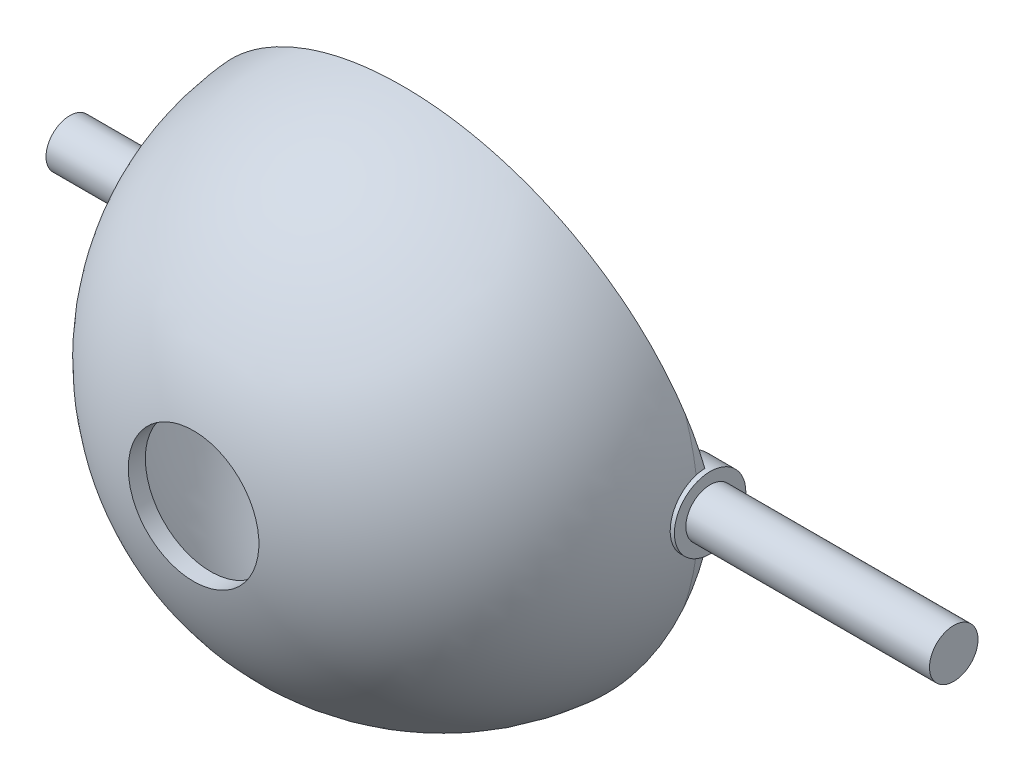
SolidWorks part; units mm, degrees
ref_plane "Front Plane" through (0, 0, 0) normal (0, 0, 1) x (1, 0, 0)
ref_plane "Top Plane" through (0, 0, 0) normal (0, 1, 0) x (1, 0, 0)
ref_plane "Right Plane" through (0, 0, 0) normal (1, 0, 0) x (0, 0, -1)
sketch "Sketch1" plane through (0, 0, 0) normal (0, 0, 1) x (1, 0, 0)
  circle A0 centre (0, 0) radius 27.95
extrude "Boss-Extrude1" add sketch "Sketch1" along normal blind 27.6202
fillet "Fillet1" radius 26.67 1 edges at (27.95, 0, 27.6202)
shell "Shell1" thickness 1.778
sketch "Sketch3" plane through (0, 0, 0) normal (0, 0, -1) x (-1, 0, 0)
  line L1 (-28.5123, -1.3772) -> (-25.5345, -1.3772)
  line L2 (-28.5123, -1.3772) -> (-28.5123, 1.3772)
  line L3 (-28.5123, 1.3772) -> (-25.5345, 1.3772)
  line L4 (-25.5345, -1.3772) -> (-25.5345, 1.3772)
  line L5 (-28.5123, -1.3772) -> (-25.5345, 1.3772) construction
  line L6 (-28.5123, 1.3772) -> (-25.5345, -1.3772) construction
  point P0 (-27.0234, 0)
extrude "Boss-Extrude3" add sketch "Sketch3" along normal blind 1.016
sketch "Sketch4" plane through (28.5123, 0, 0) normal (1, 0, 0) x (0, 0, -1)
  circle A0 centre (0, 0) radius 3.8203
extrude "Boss-Extrude4" add sketch "Sketch4" against normal blind 68.7609 and the other way blind 25.7903 contours A0
sketch "Sketch5" plane through (-40.2486, 0, 0) normal (-1, 0, 0) x (0, 0, 1)
  circle A1 centre (0, 0) radius 1.0579
extrude "Cut-Extrude1" cut sketch "Sketch5" against normal blind 74.422
sketch "Sketch6" plane through (-40.2486, 0, 0) normal (-1, 0, 0) x (0, 0, 1)
  circle A0 centre (0, 0) radius 4.4527
  circle A1 centre (0, 0) radius 2.5419
extrude "Cut-Extrude2" cut sketch "Sketch6" against normal blind 12.446 contours A1 | A0
sketch "Sketch7" plane through (54.3025, 0, 0) normal (1, 0, 0) x (0, 0, -1)
  circle A0 centre (0, 0) radius 4.5798
  circle A1 centre (0, 0) radius 2.5953
extrude "Cut-Extrude3" cut sketch "Sketch7" against normal blind 26.058 contours A1 | A0
sketch "Sketch9" plane through (0, 0, 0) normal (0, 0, -1) x (-1, 0, 0)
  circle A0 centre (0, 0) radius 25.3275
extrude "Cut-Extrude4" cut sketch "Sketch9" against normal blind 4.572 and the other way blind 8.128
sketch "Sketch10" plane through (0, 0, 27.6202) normal (0, 0, 1) x (1, 0, 0)
  circle A0 centre (0, 0) radius 6.985
extrude "Cut-Extrude5" cut sketch "Sketch10" against normal blind 5.588 contours A0
sketch3d "3DSketch1"
  circle A0 centre (0, 0, 27.0029) radius 6.985 construction
  point P2 (0, 0, 33.9879)
sketch "Sketch11" plane through (0, 0, 27.0029) normal (0, 0, 1) x (1, 0, 0)
  circle A0 centre (0, 0) radius 0.9577
extrude "Boss-Extrude5" add sketch "Sketch11" against normal blind 22.86 separate body contours A0
sketch "Sketch12" plane through (0, 0, 4.1429) normal (0, 0, -1) x (-1, 0, 0)
  line L0 (0, 0) -> (0, 16.6384)
  line L1 (0, 16.6384) -> (11.938, 16.6384)
  line L2 (0, 0) -> (0, -16.6384)
  line L3 (0, -16.6384) -> (-11.9535, -16.6384)
  circle A0 centre (11.938, 16.6384) radius 3.048
  circle A1 centre (-11.9535, -16.6384) radius 3.048
extrude "Boss-Extrude6" add sketch "Sketch12" against normal blind 11.3629 separate body contours A0 | A1
sketch "Sketch14" plane through (0, 0, 0) normal (0, 0, -1) x (-1, 0, 0)
  circle A0 centre (0, 0) radius 27.95
  circle A1 centre (0, 0) radius 2.1119
extrude "Cut-Extrude6" cut sketch "Sketch14" against normal blind 33.274 contours A1
sketch "Sketch15" plane through (54.3025, 0, 0) normal (1, 0, 0) x (0, 0, -1)
  line L0 (0, 3.8203) -> (-4.8913, 29.145)
  line L1 (-4.8913, 29.145) -> (1.6598, 29.145)
  line L2 (1.6598, 29.145) -> (0, 3.8203)
  circle A0 centre (0, 0) radius 3.8203 construction
extrude "Cut-Extrude7" cut sketch "Sketch15" against normal blind 85.2783
sketch "Sketch16" plane through (54.3025, 0, 0) normal (1, 0, 0) x (0, 0, -1)
  line L0 (0, -3.8203) -> (-4.2889, -28.4863)
  line L1 (-4.2889, -28.4863) -> (3.8203, -28.4863)
  line L2 (3.8203, -28.4863) -> (0, -3.8203)
extrude "Cut-Extrude8" cut sketch "Sketch16" against normal blind 91.8819
sketch "Sketch17" plane through (0, 0, 4.1429) normal (0, 0, -1) x (-1, 0, 0)
  line L0 (9.7719, 18.7827) -> (13.3199, 22.3667)
  line L1 (13.3199, 22.3667) -> (14.0611, 21.919)
  line L2 (14.0611, 21.919) -> (14.6047, 15.1621)
  line L3 (14.6047, 15.1621) -> (9.7719, 18.7827)
  circle A0 centre (11.938, 16.6384) radius 3.048 construction
  spline S0 degree 3 poles (24.6695, 8.7401) (24.2236, 9.9988) (23.684, 11.2069) (22.4257, 13.5261) (21.7069, 14.6372) (20.4903, 16.229) (20.061, 16.7473) (19.1708, 17.7407) (18.7082, 18.2182) (17.2689, 19.5942) (16.241, 20.4365) (14.595, 21.5856) (14.0264, 21.951) (12.8664, 22.6343) (12.2763, 22.952) (10.4762, 23.8345) (9.2368, 24.3295) (7.3183, 24.9316) (6.6688, 25.1087) (5.3496, 25.4147) (4.6853, 25.5421) (2.6925, 25.8467) (1.3581, 25.9482) (-0.652, 25.9495) (-1.3234, 25.9247) (-2.6693, 25.8235) (-3.3456, 25.7466) (-5.345, 25.4417) (-6.6489, 25.1397) (-8.5621, 24.5421) (-9.1927, 24.3187) (-10.4395, 23.8227) (-11.0575, 23.5491) (-12.8758, 22.6588) (-15.1772, 21.3023) (-17.2413, 19.6189) (-18.6973, 18.2294) (-19.1652, 17.7465) (-20.0546, 16.7548) (-20.4779, 16.2441) (-21.6847, 14.6684) (-22.4055, 13.56) (-23.3585, 11.8086) (-23.6553, 11.2081) (-24.199, 9.9889) (-24.4465, 9.3695) (-24.6695, 8.7401) knots 0 0 0 0 0.0625 0.0625 0.125 0.125 0.15625 0.15625 0.1875 0.1875 0.25 0.25 0.28125 0.28125 0.3125 0.3125 0.375 0.375 0.40625 0.40625 0.4375 0.4375 0.5 0.5 0.53125 0.53125 0.5625 0.5625 0.625 0.625 0.65625 0.65625 0.6875 0.6875 0.75 0.8125 0.8125 0.84375 0.84375 0.875 0.875 0.9375 0.9375 0.96875 0.96875 1 1 1 1 construction
extrude "Boss-Extrude7" add sketch "Sketch17" against normal blind 4.318
sketch "Sketch18" plane through (0, 0, 4.1429) normal (0, 0, -1) x (-1, 0, 0)
  line L0 (-14.4605, -14.9047) -> (-17.7671, -19.6864)
  line L1 (-17.7671, -19.6864) -> (-12.9198, -22.6359)
  line L2 (-12.9198, -22.6359) -> (-9.4465, -18.372)
  line L3 (-9.4465, -18.372) -> (-14.4605, -14.9047)
  circle A0 centre (-11.9535, -16.6384) radius 3.048 construction
  spline S0 degree 3 poles (-24.4696, -9.2851) (-24.003, -10.5148) (-23.4474, -11.6935) (-22.1656, -13.9533) (-21.4394, -15.0344) (-20.2188, -16.5808) (-19.7886, -17.0847) (-18.8984, -18.0505) (-18.4368, -18.5144) (-17.0036, -19.8503) (-15.9839, -20.6667) (-14.3569, -21.7791) (-13.7969, -22.1318) (-12.649, -22.7951) (-12.0658, -23.1031) (-10.2891, -23.9583) (-9.0686, -24.437) (-7.1841, -25.0185) (-6.5469, -25.1895) (-5.2541, -25.4846) (-4.5983, -25.6085) (-2.6367, -25.9035) (-1.3256, -26.0011) (0.6458, -26.002) (1.3037, -25.9779) (2.6213, -25.8802) (3.2833, -25.8061) (5.2542, -25.5101) (7.821, -24.9236) (10.2697, -23.967) (12.0604, -23.1061) (12.6481, -22.7955) (13.7884, -22.1368) (14.3435, -21.7876) (15.9641, -20.6814) (16.9854, -19.866) (18.4271, -18.524) (18.8945, -18.0546) (19.7873, -17.0864) (20.2125, -16.5882) (21.4259, -15.0527) (22.1524, -13.9744) (23.1181, -12.2751) (23.4192, -11.6949) (23.9788, -10.5064) (24.2363, -9.9) (24.4696, -9.2851) knots 0 0 0 0 0.0625 0.0625 0.125 0.125 0.15625 0.15625 0.1875 0.1875 0.25 0.25 0.28125 0.28125 0.3125 0.3125 0.375 0.375 0.40625 0.40625 0.4375 0.4375 0.5 0.5 0.53125 0.53125 0.5625 0.5625 0.625 0.6875 0.6875 0.71875 0.71875 0.75 0.75 0.8125 0.8125 0.84375 0.84375 0.875 0.875 0.9375 0.9375 0.96875 0.96875 1 1 1 1 construction
extrude "Boss-Extrude8" add sketch "Sketch18" against normal blind 4.572
